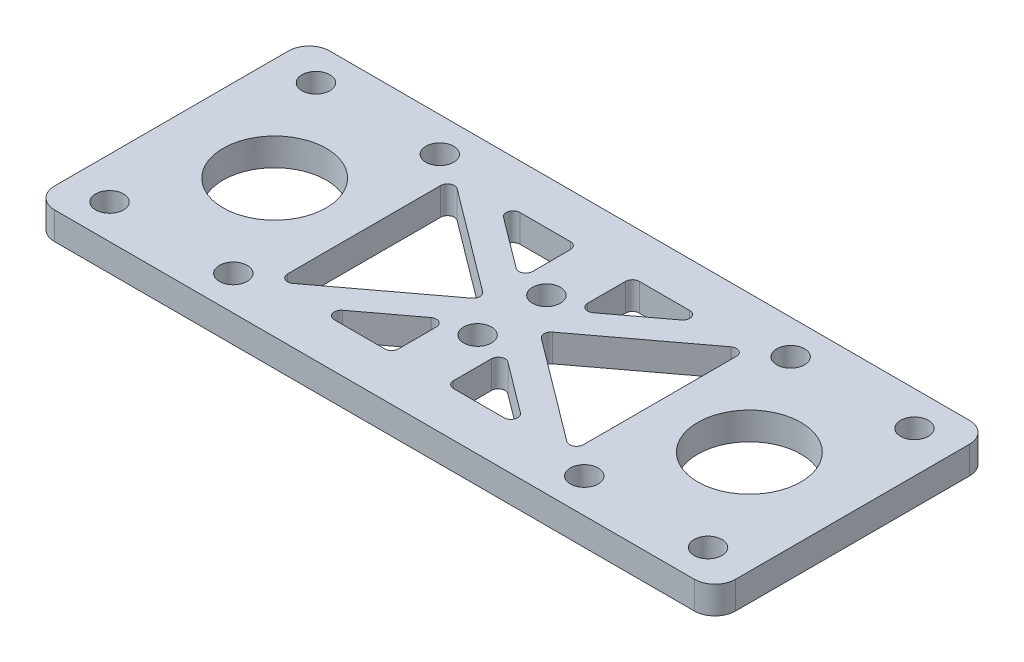
SolidWorks part; units mm, degrees
material "Thornel Mat VMA"
ref_plane "前视基准面" through (0, 0, 0) normal (0, 0, 1) x (1, 0, 0)
ref_plane "上视基准面" through (0, 0, 0) normal (0, 1, 0) x (1, 0, 0)
ref_plane "右视基准面" through (0, 0, 0) normal (1, 0, 0) x (0, 0, -1)
other "Configuration Table"
sketch "草图1" plane through (0, 0, 0) normal (0, 1, 0) x (1, 0, 0)
  line L1 (-49.5, -20) -> (49.5, -20)
  line L2 (-49.5, -20) -> (-49.5, 20)
  line L3 (-49.5, 20) -> (49.5, 20)
  line L4 (49.5, -20) -> (49.5, 20)
  line L5 (-49.5, -20) -> (49.5, 20) construction
  line L6 (-49.5, 20) -> (49.5, -20) construction
  point P0 (0, 0)
  dimension "D1" = 99
  dimension "D2" = 40
extrude "凸台-拉伸1" add sketch "草图1" along normal blind 4
sketch "草图2" plane through (0, 4, 0) normal (0, 1, 0) x (1, 0, 0)
  line L0 (-49.5, 20) -> (-49.5, -20) construction
  line L1 (-43.5, -15) -> (-25.5, -15) construction
  line L2 (-43.5, -15) -> (-43.5, 15) construction
  line L3 (-43.5, 15) -> (-25.5, 15) construction
  line L4 (-25.5, -15) -> (-25.5, 15) construction
  line L5 (-43.5, -15) -> (-25.5, 15) construction
  line L6 (-43.5, 15) -> (-25.5, -15) construction
  circle A0 centre (-43.5, 15) radius 2.025
  circle A1 centre (-43.5, -15) radius 2.025
  circle A2 centre (-25.5, -15) radius 2.025
  circle A3 centre (-25.5, 15) radius 2.025
  point P0 (-34.5, 0)
  dimension "D4" = 4.05
  dimension "D1" = 30
  dimension "D2" = 18
  dimension "D3" = 6
extrude "切除-拉伸1" cut sketch "草图2" against normal blind 4
mirror "镜向1" about plane through (0, 0, 0) normal (1, 0, 0) of "切除-拉伸1"
fillet "圆角1" radius 3 4 edges at (49.5, 2, 20) (-49.5, 2, -20) (49.5, 2, -20) (-49.5, 2, 20)
sketch "草图3" plane through (0, 4, 0) normal (0, 1, 0) x (1, 0, 0)
  line L0 (-15.3333, 13.5) -> (15.3333, 13.5)
  line L1 (-20, -15) -> (20, -15) construction
  line L2 (-20, -15) -> (-20, 15) construction
  line L3 (-20, 15) -> (20, 15) construction
  line L4 (20, -15) -> (20, 15) construction
  line L5 (-20, -15) -> (20, 15) construction
  line L6 (-20, 15) -> (20, -15) construction
  line L7 (15.3333, 13.5) -> (0, 2)
  line L8 (0, 2) -> (-15.3333, 13.5)
  line L9 (-21.5, 13.125) -> (-21.5, -13.125)
  line L10 (-21.5, -13.125) -> (-4, 0)
  line L11 (-4, 0) -> (-21.5, 13.125)
  line L12 (0, 0) -> (0, 2) construction
  line L13 (0, 0) -> (-4, 0) construction
  line L14 (-15.3333, -13.5) -> (15.3333, -13.5)
  line L15 (15.3333, -13.5) -> (0, -2)
  line L16 (0, -2) -> (-15.3333, -13.5)
  line L17 (21.5, 13.125) -> (21.5, -13.125)
  line L18 (21.5, -13.125) -> (4, 0)
  line L19 (4, 0) -> (21.5, 13.125)
  point P0 (0, 0)
  dimension "D1" = 40
  dimension "D2" = 30
  dimension "D3" = 3
  dimension "D4" = 1.5
  dimension "D5" = 4
  dimension "D6" = 2
extrude "切除-拉伸2" cut sketch "草图3" against normal up to surface (4 mm away) up to face at (43.5, 0, -12.975)
fillet "圆角2" radius 1 12 edges at (0, 2, -2) (-15.3333, 2, -13.5) (15.3333, 2, -13.5) (4, 2, 0) (21.5, 2, -13.125) (21.5, 2, 13.125) (-21.5, 2, -13.125) (-4, 2, 0) (-15.3333, 2, 13.5) (0, 2, 2) (15.3333, 2, 13.5) (-21.5, 2, 13.125)
sketch "草图4" plane through (0, 4, 0) normal (0, 1, 0) x (1, 0, 0)
  line L1 (-43.5, 15) -> (-25.5, 15) construction
  line L2 (-43.5, 15) -> (-43.5, -15) construction
  line L3 (-43.5, -15) -> (-25.5, -15) construction
  line L4 (-25.5, 15) -> (-25.5, -15) construction
  circle A0 centre (-34.5, 0) radius 7.5
  point P9 (-34.5, -15)
  dimension "D1" = 15
extrude "切除-拉伸3" cut sketch "草图4" against normal up to surface (4 mm away) up to face at (0, 0, 9.2554)
mirror "镜向2" about plane through (0, 0, 0) normal (1, 0, 0) of "切除-拉伸3"
sketch "草图5" plane through (0, 4, 0) normal (0, 1, 0) x (1, 0, 0)
  line L0 (12.3333, 13.5) -> (-12.3333, 13.5) construction
  line L1 (-4, -13.5) -> (4, -13.5)
  line L2 (-4, -13.5) -> (-4, 13.5)
  line L3 (-4, 13.5) -> (4, 13.5)
  line L4 (4, -13.5) -> (4, 13.5)
  line L5 (-4, -13.5) -> (4, 13.5) construction
  line L6 (-4, 13.5) -> (4, -13.5) construction
  point P0 (0, 0)
  dimension "D1" = 8
extrude "凸台-拉伸2" add sketch "草图5" against normal up to surface (4 mm away) up to face at (34.5, 0, -7.5)
sketch "草图6" plane through (0, 4, 0) normal (0, 1, 0) x (1, 0, 0)
  line L0 (0, 0) -> (4.6667, 0) construction
  circle A0 centre (0, 5) radius 2.025
  circle A1 centre (0, -5) radius 2.025
  arc A2 (5.0667, 0.8) -> (5.0667, -0.8) centre (5.6667, 0) ccw construction
  dimension "D1" = 4.05
  dimension "D2" = 10
extrude "切除-拉伸4" cut sketch "草图6" against normal up to surface (4 mm away) up to face at (-8.4788, 0, -10.9791)
fillet "圆角3" radius 1 8 edges at (-4, 2, 13.5) (-4, 2, 5) (4, 2, -13.5) (4, 2, -5) (4, 2, 13.5) (4, 2, 5) (-4, 2, -13.5) (-4, 2, -5)
